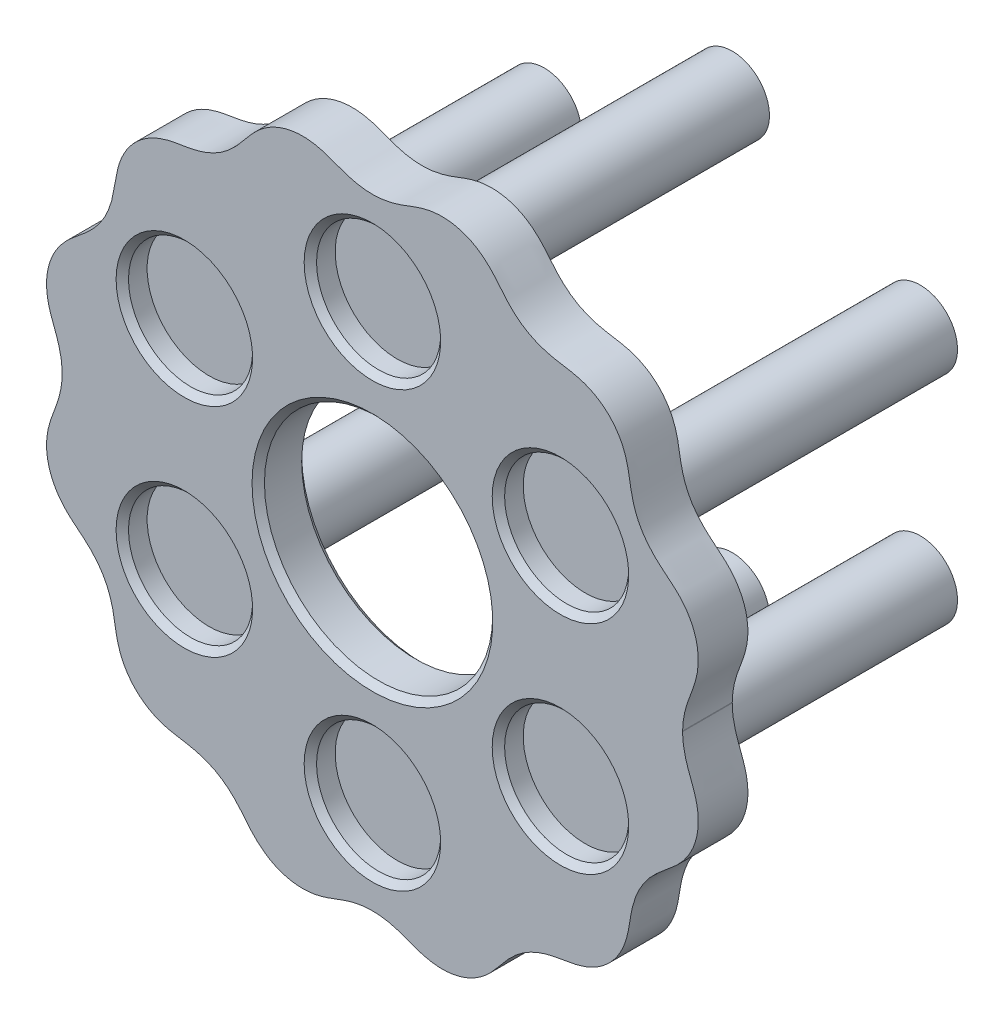
SolidWorks part; units mm, degrees
material "Polylactic Acid (PLA)"
ref_plane "Front Plane" through (0, 0, 0) normal (0, 0, 1) x (1, 0, 0)
ref_plane "Top Plane" through (0, 0, 0) normal (0, 1, 0) x (1, 0, 0)
ref_plane "Right Plane" through (0, 0, 0) normal (1, 0, 0) x (0, 0, -1)
sketch "Sketch3" plane through (0, 0, 0) normal (0, 0, 1) x (1, 0, 0)
  circle A0 centre (0, 0) radius 9.2
  circle A1 centre (0, 0) radius 17.5 construction
  circle A2 centre (0, 17.5) radius 5 construction
  circle A3 centre (15.1554, 8.75) radius 5 construction
  circle A4 centre (15.1554, -8.75) radius 5 construction
  circle A5 centre (0, -17.5) radius 5 construction
  circle A6 centre (-15.1554, -8.75) radius 5 construction
  circle A7 centre (-15.1554, 8.75) radius 5 construction
  spline S0 degree 4 poles (21.1908, 13.4898) (21.2856, 13.2293) (21.5047, 12.7166) (21.9256, 11.9944) (22.6531, 11.1441) (23.6487, 10.2926) (24.8547, 9.373) (25.8136, 8.0448) (26.2513, 6.5807) (26.291, 5.362) (26.1425, 4.3728) (25.9222, 3.637) (25.662, 2.971) (25.4535, 2.4089) (25.3271, 2.03) (25.2348, 1.7101) (25.1694, 1.4518) (25.1138, 1.1915) (25.0684, 0.9287) (25.0339, 0.6638) (25.0136, 0.4392) (25.0034, 0.2182) (24.9998, 0.0511) (24.9998, -0.0519) (25.0027, -0.1861) (25.0086, -0.3317) (25.0175, -0.4711) (25.0292, -0.6041) (25.0438, -0.7358) (25.0613, -0.8682) (25.0866, -1.0342) (25.1223, -1.2324) (25.1717, -1.4616) (25.2379, -1.7216) (25.3315, -2.0435) (25.4377, -2.3615) (25.5528, -2.6764) (25.6953, -3.0525) (25.8373, -3.4288) (26.0075, -3.9196) (26.1691, -4.5364) (26.293, -5.4006) (26.2489, -6.5093) (25.9006, -7.7589) (25.2509, -8.824) (24.5594, -9.5488) (23.8729, -10.1329) (23.242, -10.6335) (22.5405, -11.262) (21.8598, -12.0935) (21.3371, -13.0271) (20.9865, -14.0322) (20.7832, -15.0691) (20.6292, -16.2106) (20.2958, -17.4236) (19.6201, -18.6144) (18.5782, -19.6482) (17.3773, -20.3163) (16.1515, -20.64) (14.7399, -20.8265) (13.4394, -21.1259) (12.2371, -21.7311) (11.2173, -22.5863) (10.5105, -23.3824) (9.8039, -24.3012) (8.9125, -25.2023) (7.7314, -25.9117) (6.3093, -26.2999) (4.9316, -26.2885) (3.7061, -25.9646) (2.6337, -25.523) (1.6267, -25.1818) (0.5814, -24.9891) (-0.4789, -24.9807) (-1.521, -25.1546) (-2.5204, -25.4795) (-3.4192, -25.8479) (-4.2744, -26.1194) (-5.0841, -26.2552) (-5.8272, -26.2778) (-6.7511, -26.1767) (-7.8194, -25.8504) (-8.8645, -25.242) (-9.7745, -24.3376) (-10.489, -23.4094) (-11.1981, -22.6045) (-12.0193, -21.9108) (-12.9507, -21.3713) (-13.9612, -21.0044) (-15.0125, -20.7907) (-16.1735, -20.6366) (-17.4128, -20.3041) (-18.6216, -19.6172) (-19.5352, -18.6909) (-20.1095, -17.7445) (-20.4683, -16.8114) (-20.6693, -15.9295) (-20.8004, -14.9513) (-21.0215, -13.8975) (-21.3995, -12.8918) (-21.9457, -11.9715) (-22.6396, -11.1645) (-23.4354, -10.4692) (-24.3471, -9.7654) (-25.2322, -8.8715) (-25.9257, -7.6947) (-26.3017, -6.2829) (-26.2854, -4.917) (-25.9623, -3.7014) (-25.5242, -2.6362) (-25.1845, -1.6355) (-24.9896, -0.5891) (-24.9797, 0.481) (-25.1578, 1.5405) (-25.4952, 2.5629) (-25.8707, 3.4757) (-26.1355, 4.3406) (-26.2885, 5.3286) (-26.2611, 6.43) (-25.9336, 7.6784) (-25.2377, 8.8666) (-24.345, 9.7676) (-23.427, 10.4756) (-22.627, 11.1764) (-21.9369, 11.9843) (-21.3977, 12.8977) (-21.0267, 13.8865) (-20.8061, 14.9146) (-20.653, 16.0603) (-20.3956, 17.1161) (-19.9569, 18.0284) (-19.3001, 18.9288) (-18.4837, 19.6923) (-17.4358, 20.2946) (-16.1976, 20.6324) (-15.0368, 20.7873) (-13.9849, 20.9979) (-12.9731, 21.361) (-12.0395, 21.8966) (-11.2157, 22.5872) (-10.504, 23.3902) (-9.7903, 24.3186) (-8.8841, 25.2269) (-7.6859, 25.9322) (-6.4273, 26.2622) (-5.3206, 26.2881) (-4.3329, 26.1336) (-3.4683, 25.8679) (-2.5556, 25.4923) (-1.5328, 25.1559) (-0.4731, 24.979) (0.597, 24.9904) (1.6431, 25.1866) (2.6435, 25.5272) (3.7088, 25.9651) (4.9249, 26.2864) (6.2909, 26.3007) (7.702, 25.9226) (8.8779, 25.2273) (9.7704, 24.341) (10.4741, 23.4292) (11.1701, 22.634) (11.978, 21.941) (12.899, 21.3961) (13.9051, 21.0193) (14.9591, 20.7992) (15.9373, 20.6681) (16.819, 20.466) (17.7516, 20.1059) (18.6971, 19.5302) (19.6221, 18.6152) (20.3072, 17.4054) (20.6379, 16.1657) (20.7918, 15.0047) (21.0066, 13.9535) (21.3747, 12.9435) (21.9154, 12.0128) (22.6101, 11.1925) (23.4156, 10.4841) (24.3437, 9.7696) (25.2468, 8.858) (25.9409, 7.6621) (26.2625, 6.4138) (26.2848, 5.4123) (26.1914, 4.7043) (26.0881, 4.2266) (25.9672, 3.8023) (25.8079, 3.3457) (25.6196, 2.8553) (25.4588, 2.4245) (25.3339, 2.0507) (25.2417, 1.7354) (25.1764, 1.4809) (25.1203, 1.2244) (25.0741, 0.9651) (25.0385, 0.7047) (25.017, 0.4825) (25.0053, 0.2643) (25.0004, 0.1004) (24.9996, -0.0012) (25.0018, -0.1656) (25.01, -0.3844) (25.028, -0.6072) (25.0597, -0.8689) (25.1021, -1.1294) (25.1679, -1.4517) (25.266, -1.8346) (25.4047, -2.2742) (25.5863, -2.7686) (25.7756, -3.26) (25.9402, -3.7196) (26.0686, -4.1508) (26.1813, -4.6424) (26.2599, -5.1966) (26.2771, -5.8503) (26.1868, -6.6388) (25.9656, -7.4497) (25.5952, -8.2566) (25.0637, -9.0243) (24.3767, -9.7304) (23.5662, -10.3704) (22.7327, -11.0654) (21.9759, -11.9212) (21.5356, -12.6558) (21.307, -13.1772) (21.208, -13.4432) knots 0 0 0 0 0 0.005467 0.010935 0.016402 0.021869 0.031276 0.040682 0.047884 0.051484 0.055085 0.060328 0.062949 0.065571 0.066882 0.068192 0.069503 0.070814 0.072125 0.073435 0.074746 0.075401 0.076057 0.076717 0.077377 0.078036 0.078696 0.079356 0.080016 0.080676 0.081336 0.082656 0.083975 0.085295 0.086615 0.089254 0.090574 0.091894 0.094534 0.097173 0.100798 0.104424 0.111675 0.118848 0.126022 0.128665 0.131308 0.136594 0.14188 0.147166 0.152358 0.157549 0.16274 0.167931 0.175042 0.182153 0.189327 0.1965 0.201723 0.206946 0.217392 0.222615 0.227838 0.233061 0.238284 0.245457 0.252631 0.259805 0.266978 0.272201 0.277424 0.282647 0.287869 0.29303 0.29819 0.30335 0.30851 0.31216 0.31581 0.319459 0.323109 0.330383 0.337658 0.342925 0.348192 0.35346 0.358727 0.363994 0.369262 0.374529 0.379796 0.387071 0.394345 0.401519 0.405106 0.408692 0.413978 0.419265 0.424551 0.429837 0.435028 0.440219 0.44541 0.450602 0.457712 0.464823 0.471934 0.479045 0.484236 0.489427 0.494619 0.49981 0.505096 0.510382 0.515668 0.520954 0.524541 0.528128 0.535301 0.542475 0.549649 0.554872 0.560094 0.565317 0.57054 0.5757 0.58086 0.58602 0.591181 0.59848 0.60213 0.605779 0.613054 0.620328 0.625595 0.630863 0.63613 0.641397 0.646665 0.651932 0.657199 0.662467 0.669741 0.677015 0.684189 0.687776 0.691363 0.696649 0.701935 0.707221 0.712507 0.717698 0.722889 0.728081 0.733272 0.740383 0.747494 0.754604 0.761715 0.766906 0.772098 0.777289 0.78248 0.787766 0.793052 0.798338 0.803624 0.807211 0.810798 0.817972 0.825246 0.83252 0.837788 0.843055 0.848322 0.85359 0.858857 0.864124 0.869392 0.874659 0.881933 0.889208 0.896232 0.899744 0.9015 0.903256 0.905842 0.908428 0.911014 0.9136 0.914893 0.916186 0.917479 0.918772 0.920065 0.921358 0.922651 0.923297 0.923944 0.924592 0.92524 0.926536 0.927831 0.929127 0.930423 0.931719 0.934311 0.936903 0.939495 0.942087 0.944679 0.946512 0.948345 0.952012 0.955678 0.959345 0.963918 0.968492 0.973065 0.977639 0.983229 0.988819 0.99441 1 1 1 1 1 construction
  spline S1 degree 4 poles (25, 0) (25, -0.0284) (25.0005, -0.0852) (25.0027, -0.1861) (25.0086, -0.3317) (25.0175, -0.4711) (25.0292, -0.6041) (25.0438, -0.7358) (25.0613, -0.8682) (25.0866, -1.0342) (25.1223, -1.2324) (25.1717, -1.4616) (25.2379, -1.7216) (25.3315, -2.0435) (25.4377, -2.3615) (25.5528, -2.6764) (25.6953, -3.0525) (25.8373, -3.4288) (26.0075, -3.9196) (26.1691, -4.5364) (26.293, -5.4006) (26.2489, -6.5093) (25.9006, -7.7589) (25.2509, -8.824) (24.5594, -9.5488) (23.8729, -10.1329) (23.242, -10.6335) (22.5405, -11.262) (21.8598, -12.0935) (21.3371, -13.0271) (20.9865, -14.0322) (20.7832, -15.0691) (20.6292, -16.2106) (20.2958, -17.4236) (19.6201, -18.6144) (18.5782, -19.6482) (17.3773, -20.3163) (16.1515, -20.64) (14.7399, -20.8265) (13.4394, -21.1259) (12.2371, -21.7311) (11.2173, -22.5863) (10.5105, -23.3824) (9.8039, -24.3012) (8.9125, -25.2023) (7.7314, -25.9117) (6.3093, -26.2999) (4.9316, -26.2885) (3.7061, -25.9646) (2.6337, -25.523) (1.6267, -25.1818) (0.5814, -24.9891) (-0.4789, -24.9807) (-1.521, -25.1546) (-2.5204, -25.4795) (-3.4192, -25.8479) (-4.2744, -26.1194) (-5.0841, -26.2552) (-5.8272, -26.2778) (-6.7511, -26.1767) (-7.8194, -25.8504) (-8.8645, -25.242) (-9.7745, -24.3376) (-10.489, -23.4094) (-11.1981, -22.6045) (-12.0193, -21.9108) (-12.9507, -21.3713) (-13.9612, -21.0044) (-15.0125, -20.7907) (-16.1735, -20.6366) (-17.4128, -20.3041) (-18.6216, -19.6172) (-19.5352, -18.6909) (-20.1095, -17.7445) (-20.4683, -16.8114) (-20.6693, -15.9295) (-20.8004, -14.9513) (-21.0215, -13.8975) (-21.3995, -12.8918) (-21.9457, -11.9715) (-22.6396, -11.1645) (-23.4354, -10.4692) (-24.3471, -9.7654) (-25.2322, -8.8715) (-25.9257, -7.6947) (-26.3017, -6.2829) (-26.2854, -4.917) (-25.9623, -3.7014) (-25.5242, -2.6362) (-25.1845, -1.6355) (-24.9896, -0.5891) (-24.9797, 0.481) (-25.1578, 1.5405) (-25.4952, 2.5629) (-25.8707, 3.4757) (-26.1355, 4.3406) (-26.2885, 5.3286) (-26.2611, 6.43) (-25.9336, 7.6784) (-25.2377, 8.8666) (-24.345, 9.7676) (-23.427, 10.4756) (-22.627, 11.1764) (-21.9369, 11.9843) (-21.3977, 12.8977) (-21.0267, 13.8865) (-20.8061, 14.9146) (-20.653, 16.0603) (-20.3956, 17.1161) (-19.9569, 18.0284) (-19.3001, 18.9288) (-18.4837, 19.6923) (-17.4358, 20.2946) (-16.1976, 20.6324) (-15.0368, 20.7873) (-13.9849, 20.9979) (-12.9731, 21.361) (-12.0395, 21.8966) (-11.2157, 22.5872) (-10.504, 23.3902) (-9.7903, 24.3186) (-8.8841, 25.2269) (-7.6859, 25.9322) (-6.4273, 26.2622) (-5.3206, 26.2881) (-4.3329, 26.1336) (-3.4683, 25.8679) (-2.5556, 25.4923) (-1.5328, 25.1559) (-0.4731, 24.979) (0.597, 24.9904) (1.6431, 25.1866) (2.6435, 25.5272) (3.7088, 25.9651) (4.9249, 26.2864) (6.2909, 26.3007) (7.702, 25.9226) (8.8779, 25.2273) (9.7704, 24.341) (10.4741, 23.4292) (11.1701, 22.634) (11.978, 21.941) (12.899, 21.3961) (13.9051, 21.0193) (14.9591, 20.7992) (15.9373, 20.6681) (16.819, 20.466) (17.7516, 20.1059) (18.6971, 19.5302) (19.6221, 18.6152) (20.3072, 17.4054) (20.6379, 16.1657) (20.7918, 15.0047) (21.0066, 13.9535) (21.3747, 12.9435) (21.9154, 12.0128) (22.6101, 11.1925) (23.4156, 10.4841) (24.3437, 9.7696) (25.2468, 8.858) (25.9409, 7.6621) (26.2625, 6.4138) (26.2848, 5.4123) (26.1914, 4.7043) (26.0881, 4.2266) (25.9672, 3.8023) (25.8079, 3.3457) (25.6196, 2.8553) (25.4588, 2.4245) (25.3339, 2.0507) (25.2417, 1.7354) (25.1764, 1.4809) (25.1203, 1.2244) (25.0741, 0.9651) (25.0385, 0.7047) (25.017, 0.4825) (25.0053, 0.2643) (25.0014, 0.1332) (25.0004, 0.0775) (25.0002, 0.0497) knots 0.076057 0.076057 0.076057 0.076057 0.076057 0.076717 0.077377 0.078036 0.078696 0.079356 0.080016 0.080676 0.081336 0.082656 0.083975 0.085295 0.086615 0.089254 0.090574 0.091894 0.094534 0.097173 0.100798 0.104424 0.111675 0.118848 0.126022 0.128665 0.131308 0.136594 0.14188 0.147166 0.152358 0.157549 0.16274 0.167931 0.175042 0.182153 0.189327 0.1965 0.201723 0.206946 0.217392 0.222615 0.227838 0.233061 0.238284 0.245457 0.252631 0.259805 0.266978 0.272201 0.277424 0.282647 0.287869 0.29303 0.29819 0.30335 0.30851 0.31216 0.31581 0.319459 0.323109 0.330383 0.337658 0.342925 0.348192 0.35346 0.358727 0.363994 0.369262 0.374529 0.379796 0.387071 0.394345 0.401519 0.405106 0.408692 0.413978 0.419265 0.424551 0.429837 0.435028 0.440219 0.44541 0.450602 0.457712 0.464823 0.471934 0.479045 0.484236 0.489427 0.494619 0.49981 0.505096 0.510382 0.515668 0.520954 0.524541 0.528128 0.535301 0.542475 0.549649 0.554872 0.560094 0.565317 0.57054 0.5757 0.58086 0.58602 0.591181 0.59848 0.60213 0.605779 0.613054 0.620328 0.625595 0.630863 0.63613 0.641397 0.646665 0.651932 0.657199 0.662467 0.669741 0.677015 0.684189 0.687776 0.691363 0.696649 0.701935 0.707221 0.712507 0.717698 0.722889 0.728081 0.733272 0.740383 0.747494 0.754604 0.761715 0.766906 0.772098 0.777289 0.78248 0.787766 0.793052 0.798338 0.803624 0.807211 0.810798 0.817972 0.825246 0.83252 0.837788 0.843055 0.848322 0.85359 0.858857 0.864124 0.869392 0.874659 0.881933 0.889208 0.896232 0.899744 0.9015 0.903256 0.905842 0.908428 0.911014 0.9136 0.914893 0.916186 0.917479 0.918772 0.920065 0.921358 0.922651 0.923297 0.923944 0.923944 0.923944 0.923944 0.923944
  spline S2 degree 1 poles (25.0002, 0.0497) (25, 0) knots 0 0 1 1
  point P17 (0, 0)
  dimension "D1" = 18.4
  dimension "D2" = 35
  dimension "D3" = 10
  dimension "D4" = 6
extrude "Boss-Extrude2" add sketch "Sketch3" along normal blind 4
sketch "Sketch6" plane through (0, 0, 4) normal (0, 0, 1) x (1, 0, 0)
  circle A0 centre (15.1554, -8.75) radius 5 construction
  circle A1 centre (0, -17.5) radius 5 construction
  circle A2 centre (-15.1554, -8.75) radius 5 construction
  circle A3 centre (0, 0) radius 17.5 construction
  circle A4 centre (15.1554, 8.75) radius 5 construction
  circle A5 centre (0, 17.5) radius 5 construction
  circle A6 centre (15.1554, -8.75) radius 5
  circle A7 centre (0, -17.5) radius 5
  circle A8 centre (-15.1554, -8.75) radius 5
  circle A9 centre (0, 0) radius 17.5 construction
  circle A10 centre (15.1554, 8.75) radius 5
  circle A11 centre (0, 17.5) radius 5
  circle A12 centre (-15.1554, 8.75) radius 5 construction
  circle A13 centre (-15.1554, 8.75) radius 5
sketch "Sketch7" plane through (0, 0, 0) normal (0, 0, -1) x (-1, 0, 0)
  circle A0 centre (0, 17.5) radius 3
  circle A1 centre (15.1554, 8.75) radius 3
  circle A2 centre (15.1554, -8.75) radius 3
  circle A3 centre (0, -17.5) radius 3
  circle A4 centre (-15.1554, -8.75) radius 3
  circle A5 centre (-15.1554, 8.75) radius 3
  point P15 (0, 0)
  dimension "D1" = 6
  dimension "D3" = 9.8446
  dimension "D2" = 6
extrude "Boss-Extrude3" add sketch "Sketch7" along normal blind 25
extrude "Cut-Extrude2" cut sketch "Sketch6" against normal blind 2
fillet "Fillet1" radius 1 6 edges at (-3, 17.5, 0) (-18.1554, 8.75, 0) (-18.1554, -8.75, 0) (-3, -17.5, 0) (12.1554, -8.75, 0) (12.1554, 8.75, 0)
chamfer "Chamfer1" distance 0.5 angle 45 8 edges at (20.1554, -8.75, 4) (5, -17.5, 4) (-10.1554, -8.75, 4) (-10.1554, 8.75, 4) (5, 17.5, 4) (20.1554, 8.75, 4) (9.2, 0, 4) (9.2, 0, 0)
